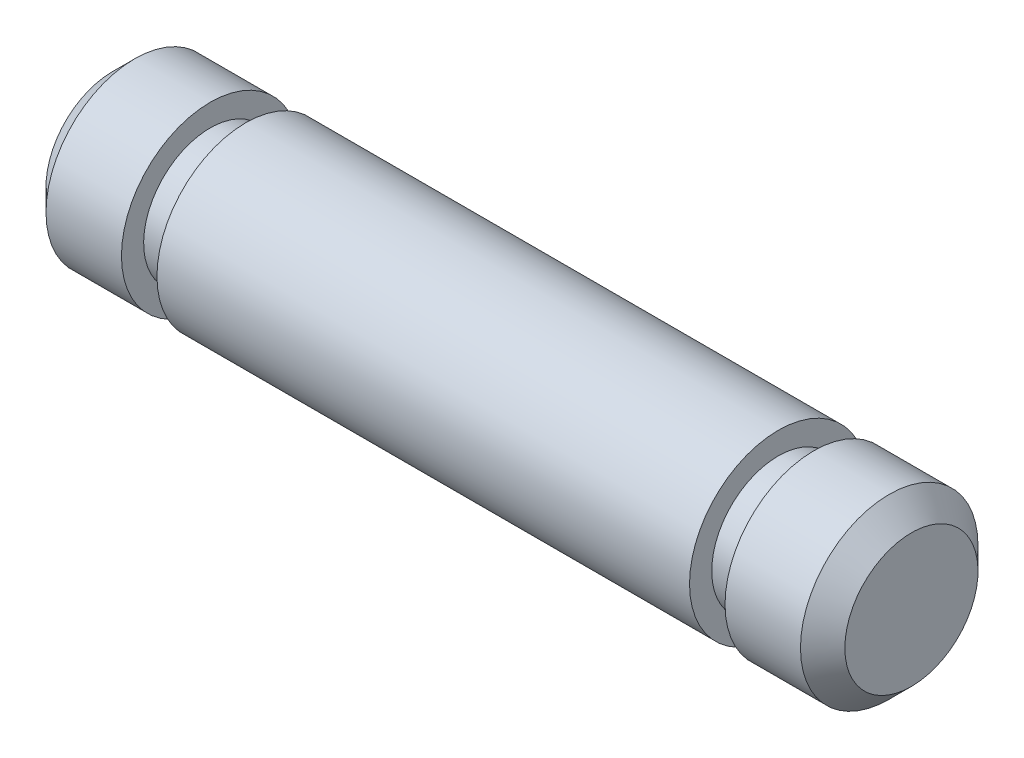
SolidWorks part; units mm, degrees
material "201.0-T6 Insulated Mold Casting (SS)"
ref_plane "Front Plane" through (0, 0, 0) normal (0, 0, 1) x (1, 0, 0)
ref_plane "Top Plane" through (0, 0, 0) normal (0, 1, 0) x (1, 0, 0)
ref_plane "Right Plane" through (0, 0, 0) normal (1, 0, 0) x (0, 0, -1)
sketch "Sketch1" plane through (0, 0, 0) normal (0, 0, 1) x (1, 0, 0)
  line L0 (0, 0) -> (18, 0)
  line L1 (18, 0) -> (18, 2)
  line L2 (18, 2) -> (0, 2)
  line L3 (0, 2) -> (0, 0)
  dimension "D1" = 18
  dimension "D2" = 2
revolve "Revolve1" add sketch "Sketch1" angle 360 about L2
sketch "Sketch2" plane through (0, 0, 0) normal (-1, 0, 0) x (0, 0, 1)
  circle A0 centre (0, 2) radius 1.5
  circle A1 centre (0, 2) radius 2
  circle A2 centre (0, 2) radius 2
  dimension "D2" = 3
  dimension "D1" = 0
extrude "Cut-Extrude1" cut sketch "Sketch2" along normal blind 0.8 from offset 3 offset against normal yes
sketch "Sketch4" plane through (18, 0, 0) normal (1, 0, 0) x (0, 0, -1)
  circle A0 centre (0, 2) radius 1.5
  circle A1 centre (0, 2) radius 2
  circle A2 centre (0, 2) radius 2
  dimension "D2" = 3
  dimension "D1" = 0
extrude "Cut-Extrude2" cut sketch "Sketch4" along normal blind 0.8 from offset 3 offset against normal yes
chamfer "Chamfer1" distance 0.5 angle 45 2 edges at (0, 4, 0) (18, 4, 0)
